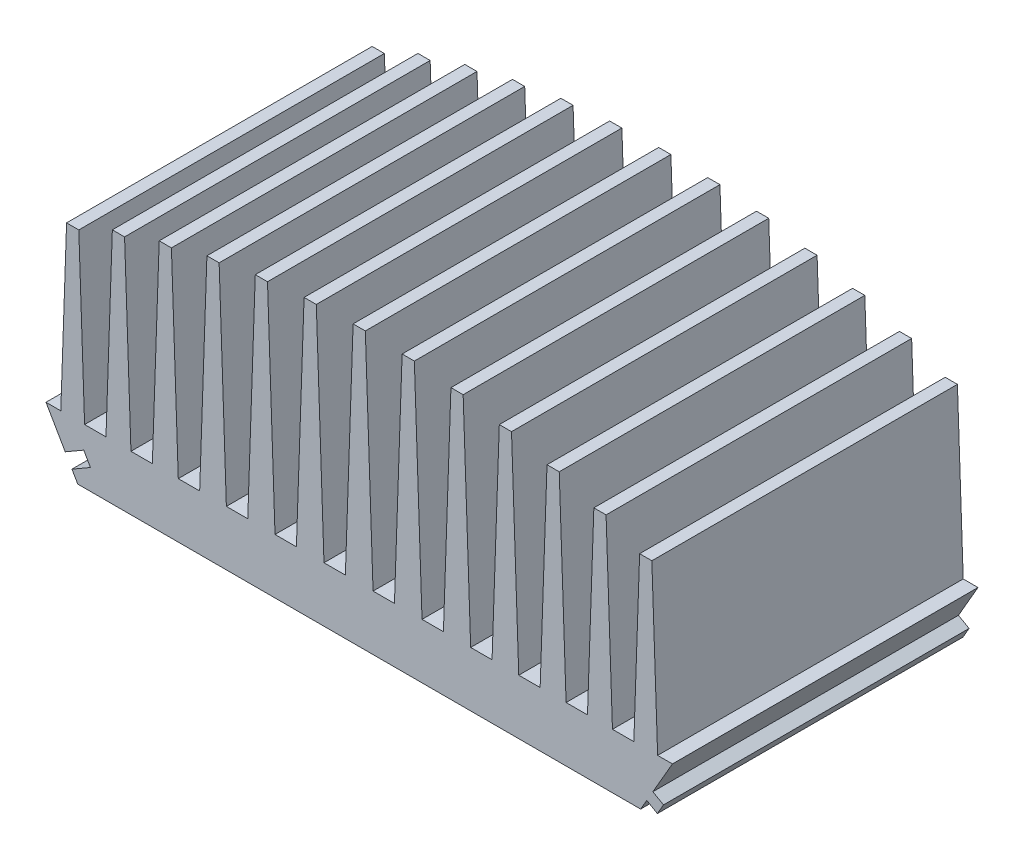
SolidWorks part; units mm, degrees
ref_plane "Plano frontal" through (0, 0, 0) normal (0, 0, 1) x (1, 0, 0)
ref_plane "Plano superior" through (0, 0, 0) normal (0, 1, 0) x (1, 0, 0)
ref_plane "Plano direito" through (0, 0, 0) normal (1, 0, 0) x (0, 0, -1)
sketch "Esboço1" plane through (0, 0, 0) normal (0, 0, 1) x (1, 0, 0)
  line L4 (0, 0) -> (-51.25, 88.7676) construction
  line L6 (-46.0538, 79.7676) -> (-51.25, 88.7676)
  line L20 (-48.8291, 88.7676) -> (-47.8825, 115.8751)
  line L21 (-47.8825, 115.8751) -> (-45.8825, 115.8751)
  line L22 (-45.8825, 115.8751) -> (-44.9359, 88.7676)
  line L23 (-44.9359, 88.7676) -> (-41.4359, 88.7676)
  line L24 (-41.4359, 88.7676) -> (-40.3931, 118.6305)
  line L25 (-40.3931, 118.6305) -> (-38.3931, 118.6305)
  line L26 (-38.3931, 118.6305) -> (-37.3502, 88.7676)
  line L27 (-37.3502, 88.7676) -> (-33.8502, 88.7676)
  line L28 (-33.8502, 88.7676) -> (-32.7279, 120.9063)
  line L29 (-32.7279, 120.9063) -> (-30.7279, 120.9063)
  line L30 (-30.7279, 120.9063) -> (-29.6056, 88.7676)
  line L31 (-29.6056, 88.7676) -> (-26.1056, 88.7676)
  line L32 (-26.1056, 88.7676) -> (-24.921, 122.6898)
  line L33 (-24.921, 122.6898) -> (-22.921, 122.6898)
  line L34 (-22.921, 122.6898) -> (-21.7364, 88.7676)
  line L37 (-21.7364, 88.7676) -> (-18.2364, 88.7676)
  line L38 (-18.2364, 88.7676) -> (-17.0071, 123.9709)
  line L39 (-17.0071, 123.9709) -> (-15.0071, 123.9709)
  line L40 (-15.0071, 123.9709) -> (-13.7778, 88.7676)
  line L42 (-13.7778, 88.7676) -> (-10.2778, 88.7676)
  line L43 (-10.2778, 88.7676) -> (-9.0215, 124.7424)
  line L44 (-9.0215, 124.7424) -> (-7.0215, 124.7424)
  line L45 (-7.0215, 124.7424) -> (-5.7653, 88.7676)
  line L46 (-5.7653, 88.7676) -> (-2.2653, 88.7676)
  line L47 (-2.2653, 88.7676) -> (-1, 125)
  line L50 (0, 0) -> (0, 125) construction
  line L90 (0, 0) -> (-140.069, 0) construction
  line L91 (-46.0538, 79.7676) -> (46.0538, 79.7676)
  line L127 (46.0538, 79.7676) -> (51.25, 88.7676)
  line L128 (2.2653, 88.7676) -> (1, 125)
  line L129 (5.7653, 88.7676) -> (2.2653, 88.7676)
  line L130 (7.0215, 124.7424) -> (5.7653, 88.7676)
  line L131 (9.0215, 124.7424) -> (7.0215, 124.7424)
  line L132 (10.2778, 88.7676) -> (9.0215, 124.7424)
  line L133 (13.7778, 88.7676) -> (10.2778, 88.7676)
  line L134 (15.0071, 123.9709) -> (13.7778, 88.7676)
  line L135 (17.0071, 123.9709) -> (15.0071, 123.9709)
  line L136 (18.2364, 88.7676) -> (17.0071, 123.9709)
  line L137 (21.7364, 88.7676) -> (18.2364, 88.7676)
  line L138 (22.921, 122.6898) -> (21.7364, 88.7676)
  line L139 (24.921, 122.6898) -> (22.921, 122.6898)
  line L140 (26.1056, 88.7676) -> (24.921, 122.6898)
  line L141 (29.6056, 88.7676) -> (26.1056, 88.7676)
  line L142 (30.7279, 120.9063) -> (29.6056, 88.7676)
  line L143 (32.7279, 120.9063) -> (30.7279, 120.9063)
  line L144 (33.8502, 88.7676) -> (32.7279, 120.9063)
  line L145 (37.3502, 88.7676) -> (33.8502, 88.7676)
  line L146 (38.3931, 118.6305) -> (37.3502, 88.7676)
  line L147 (40.3931, 118.6305) -> (38.3931, 118.6305)
  line L148 (41.4359, 88.7676) -> (40.3931, 118.6305)
  line L149 (44.9359, 88.7676) -> (41.4359, 88.7676)
  line L150 (45.8825, 115.8751) -> (44.9359, 88.7676)
  line L151 (47.8825, 115.8751) -> (45.8825, 115.8751)
  line L152 (48.8291, 88.7676) -> (47.8825, 115.8751)
  line L153 (51.25, 88.7676) -> (48.8291, 88.7676)
  line L154 (-1, 125) -> (1, 125)
  line L155 (-51.25, 88.7676) -> (-48.8291, 88.7676)
  circle A0 centre (0, 0) radius 125 construction
  point P5 (0, 125)
  point P9 (-46.8825, 115.8751)
  point P19 (0, 79.7676)
  point P68 (-39.3931, 118.6305)
  point P69 (-31.7279, 120.9063)
  point P70 (-23.921, 122.6898)
  point P71 (-16.0071, 123.9709)
  point P80 (-8.0215, 124.7424)
  dimension "D1" = 250
  dimension "D2" = 9
  dimension "D3" = 60
  dimension "D4" = 3.5
  dimension "D5" = 2
  dimension "D6" = 92
  dimension "D7" = 92
  dimension "D9" = 51.25
extrude "Ressalto-extrusão1" add sketch "Esboço1" along normal blind 285
sketch "Esboço2" plane through (0, 0, 285) normal (0, 0, 1) x (1, 0, 0)
  line L0 (-47.0038, 81.4131) -> (-43.9728, 83.1631)
  line L1 (-48.1038, 83.3183) -> (-48.0538, 83.2317) construction
  line L2 (-43.9728, 83.1631) -> (-45.0728, 85.0683)
  line L3 (-47.0538, 81.4997) -> (-47.0038, 81.4131) construction
  line L5 (-48.1038, 83.3183) -> (-45.0728, 85.0683)
  line L6 (-48.1038, 83.3183) -> (-47.0038, 81.4131)
  line L7 (-51.25, 88.7676) -> (-46.0538, 79.7676) construction
  dimension "D1" = 2
  dimension "D2" = 3.5
  dimension "D3" = 2
  dimension "D4" = 0.1
extrude "Corte-extrusão1" cut sketch "Esboço2" against normal through all
sketch "Esboço3" plane through (0, 0, 285) normal (0, 0, 1) x (1, 0, 0)
  line L1 (46.0538, 79.7676) -> (51.25, 88.7676) construction
  line L6 (47.0538, 81.4997) -> (48.0538, 83.2317)
  line L10 (48.0538, 83.2317) -> (49.7859, 82.2317)
  line L11 (49.7859, 82.2317) -> (48.7859, 80.4997)
  line L12 (48.7859, 80.4997) -> (47.0538, 81.4997)
  dimension "D1" = 2
  dimension "D2" = 2
  dimension "D3" = 2
extrude "Ressalto-extrusão3" add sketch "Esboço3" against normal blind 285 separate body
sketch "Esboço13" plane through (0, 0, 0) normal (1, 0, 0) x (0, 0, -1)
  line L0 (-285, 83.7676) -> (-283.5, 83.7676)
  line L1 (-283.5, 83.7676) -> (-283.5, 81.7676)
  line L2 (-283.5, 81.7676) -> (-285, 81.7676)
  line L3 (-285, 81.7676) -> (-285, 83.7676)
  line L4 (-285, 79.7676) -> (0, 79.7676) construction
  line L5 (-285, 85.0683) -> (-285, 83.3183) construction
  dimension "D1" = 2
  dimension "D2" = 2
  dimension "D3" = 1.5
extrude "Corte-extrusão7" cut sketch "Esboço13" against normal through all both and the other way through all
sketch "Esboço8" plane through (0, 0, 0) normal (0.866, -0.5, 0) x (0, 0, -1)
  line L0 (-280, 104.1077) -> (-280, 96.1077)
  line L1 (-280, 96.1077) -> (-270, 96.1077)
  line L2 (-270, 96.1077) -> (-270, 104.1077)
  line L4 (0, 96.1077) -> (-283.5, 96.1077) construction
  line L5 (0, 96.1077) -> (-283.5, 96.1077) construction
  line L6 (-285, 96.7265) -> (-285, 102.5) construction
  arc A0 (-280, 104.1077) -> (-270, 104.1077) centre (-275, 104.1077) cw
  dimension "D1" = 5
  dimension "D4" = 8
  dimension "D2" = 10
  dimension "D3" = 5
  dimension "D5" = 8
  dimension "D6" = 8
extrude "Ressalto-extrusão5" add sketch "Esboço8" against normal blind 10
sketch "Esboço5" plane through (0, 0, 285) normal (0, 0, 1) x (1, 0, 0)
  line L0 (-46.0538, 79.7676) -> (46.0538, 79.7676) construction
  circle A0 centre (-30, 85.2676) radius 1.25
  circle A1 centre (30, 85.2676) radius 1.25
  dimension "D1" = 2.5
  dimension "D2" = 21.25
  dimension "D3" = 5.5
  dimension "D4" = 2.5
  dimension "D5" = 21.25
  dimension "D6" = 5.5
extrude "Corte-extrusão3" cut sketch "Esboço5" against normal blind 10
sketch "Esboço6" plane through (0, 0, 0) normal (-0.866, -0.5, 0) x (0, 0, 1)
  line L0 (280, 104.2077) -> (280, 96.3093)
  line L1 (280, 96.3093) -> (270, 96.3093)
  line L2 (270, 96.3093) -> (270, 104.2077)
  line L5 (285, 102.5) -> (285, 96.7265) construction
  line L6 (0, 96.2077) -> (283.5, 96.2077) construction
  arc A0 (270, 104.2077) -> (280, 104.2077) centre (275, 104.2077) cw
  dimension "D2" = 5
  dimension "D1" = 5
  dimension "D3" = 10
  dimension "D5" = 8
extrude "Ressalto-extrusão4" add sketch "Esboço6" against normal blind 11
sketch "Esboço7" plane through (0, 0, 0) normal (-0.866, -0.5, 0) x (0, 0, 1)
  circle A0 centre (275, 104.2077) radius 2.25
  dimension "D1" = 4.5
extrude "Corte-extrusão4" cut sketch "Esboço7" against normal blind 12
sketch "Esboço9" plane through (0, 0, 0) normal (0.866, -0.5, 0) x (0, 0, -1)
  circle A0 centre (-275, 104.1077) radius 1.65
  dimension "D1" = 3.3
extrude "Corte-extrusão5" cut sketch "Esboço9" against normal blind 10
sketch "Esboço10" plane through (0, 0, 0) normal (0, 0, -1) x (-1, 0, 0)
  line L0 (9.3622, 114.9876) -> (9.3622, 88.7676)
  line L2 (9.3622, 88.7676) -> (-9.3622, 88.7676)
  line L3 (-9.3622, 88.7676) -> (-9.3622, 114.9876)
  line L4 (9.0215, 124.7424) -> (10.2778, 88.7676) construction
  line L6 (-10.2778, 88.7676) -> (-9.0215, 124.7424) construction
  line L8 (2.2653, 88.7676) -> (5.7653, 88.7676) construction
  line L10 (-9.3622, 114.9876) -> (9.3622, 114.9876)
  dimension "D1" = 26.22
extrude "Ressalto-extrusão6" add sketch "Esboço10" against normal blind 15
sketch "Esboço12" plane through (0, 0, 0) normal (0, 0, -1) x (-1, 0, 0)
  line L0 (46.0538, 79.7676) -> (-46.0538, 79.7676) construction
  line L1 (0, 125) -> (0, 79.7676) construction
  line L2 (-1, 125) -> (1, 125) construction
  circle A0 centre (0, 105) radius 2.5
  dimension "D1" = 5
  dimension "D2" = 25.2324
extrude "Corte-extrusão8" cut sketch "Esboço12" against normal blind 20
sketch "Esboço14" plane through (0, 0, 0) normal (-0.866, -0.5, 0) x (0, 0, 1)
  circle A0 centre (275, 104.2077) radius 6
  dimension "D1" = 12
extrude "Corte-extrusão9" cut sketch "Esboço14" against normal blind 100 from offset 11 offset against normal yes
pattern_linear "Padrão linear1" count 2 spacing 230 along (0, 0, -1) of "Corte-extrusão4", "Ressalto-extrusão4", "Corte-extrusão9", "Ressalto-extrusão5", "Corte-extrusão5"
sketch "Esboço15" [suppressed] plane through (0, 79.7676, 0) normal (0, -1, 0) x (1, 0, 0)
  circle A0 centre (36.5, 246.65) radius 1.65
  circle A1 centre (-36.5, 246.65) radius 1.65
  circle A2 centre (38.145, 142.066) radius 1.65
  circle A3 centre (32.5, 12.65) radius 1.65
  circle A4 centre (-38.5, 26.15) radius 1.65
  circle A5 centre (-15.83, 8.335) radius 1.25
  circle A6 centre (-15.449, 26.242) radius 1.25
  circle A7 centre (25.572, 49.15) radius 1.25
  circle A8 centre (21.762, 76.661) radius 1.25
  circle A9 centre (-25.863, 97.743) radius 1.25
  circle A10 centre (-22.307, 180.42) radius 1.25
  circle A11 centre (27.096, 173.943) radius 1.25
  circle A12 centre (21.254, 234.65) radius 1.25
  circle A13 centre (17.5, 217.65) radius 1.25
  circle A14 centre (17.5, 197.65) radius 1.25
  circle A15 centre (17.5, 177.65) radius 1.25
  circle A16 centre (17.5, 157.65) radius 1.25
  circle A17 centre (-17.5, 127.65) radius 1.25
  circle A18 centre (-17.5, 107.65) radius 1.25
  circle A19 centre (-17.5, 87.65) radius 1.25
  circle A20 centre (-17.5, 67.65) radius 1.25
  dimension "D1" = 3.3
  dimension "D2" = 2.5
extrude "Corte-extrusão10" [suppressed] cut sketch "Esboço15" against normal blind 8
sketch "Esboço16" plane through (0, 0, 0) normal (1, 0, 0) x (0, 0, -1)
  line L1 (-310.161, 154.0853) -> (-191.229, 154.0853)
  line L2 (-310.161, 154.0853) -> (-310.161, 55.6782)
  line L3 (-310.161, 55.6782) -> (-191.229, 55.6782)
  line L4 (-191.229, 154.0853) -> (-191.229, 55.6782)
  line L5 (26.8186, 148.462) -> (-141.229, 148.462)
  line L6 (26.8186, 148.462) -> (26.8186, 55.6782)
  line L7 (26.8186, 55.6782) -> (-141.229, 55.6782)
  line L8 (-141.229, 148.462) -> (-141.229, 55.6782)
  point P8 (-142.5, 55.6782)
  dimension "D1" = 50
extrude "Corte-extrusão11" cut sketch "Esboço16" against normal through all both and the other way through all
